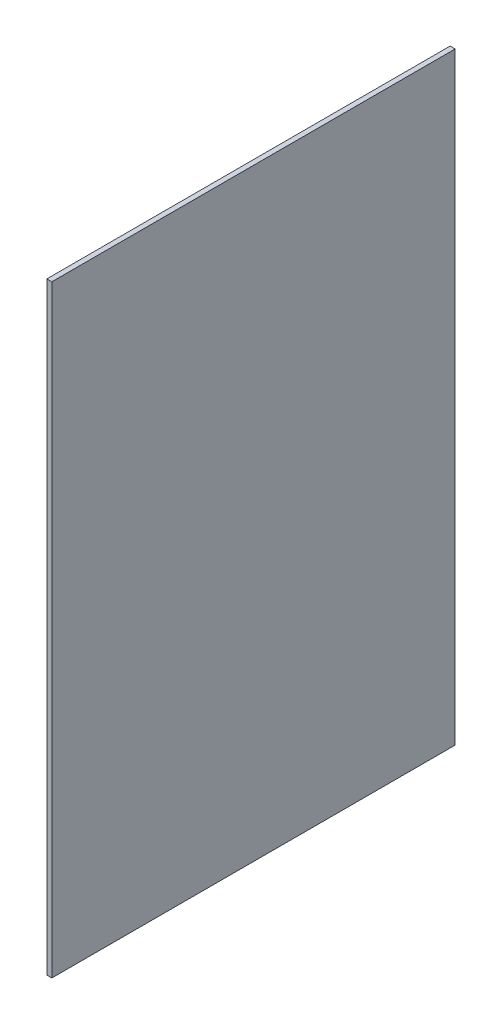
SolidWorks part; units mm, degrees
material "Plain Carbon Steel"
ref_plane "Front Plane" through (0, 0, 0) normal (0, 0, 1) x (1, 0, 0)
ref_plane "Top Plane" through (0, 0, 0) normal (0, 1, 0) x (1, 0, 0)
ref_plane "Right Plane" through (0, 0, 0) normal (1, 0, 0) x (0, 0, -1)
sketch "Sketch1" plane through (0, 0, 0) normal (0, 0, 1) x (1, 0, 0)
  line L0 (0, 0) -> (0, -177.8) construction
  line L1 (0, -177.8) -> (177.8, -177.8) construction
  line L2 (177.8, -177.8) -> (177.8, 0) construction
  line L3 (177.8, -167.8) -> (177.8, 0)
  line L4 (177.8, 0) -> (179.1945, 0)
  line L5 (179.1945, 0) -> (179.1945, -167.8)
  line L7 (177.8, -167.8) -> (179.1945, -167.8)
  circle A0 centre (0, 0) radius 177.8 construction
  dimension "D1" = 355.6
  dimension "D2" = 1.3945
  dimension "D3" = 10
extrude "Boss-Extrude1" add sketch "Sketch1" along normal blind 112.268
